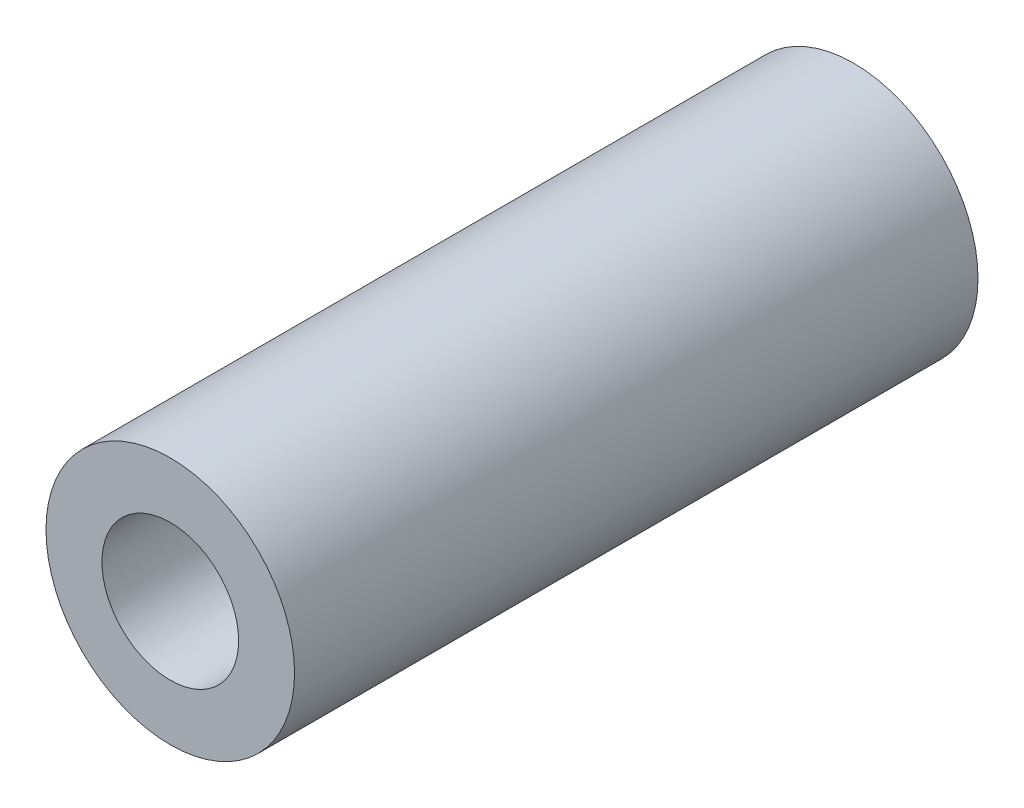
SolidWorks part; units mm, degrees
ref_plane "前视基准面" through (0, 0, 0) normal (0, 0, 1) x (1, 0, 0)
ref_plane "上视基准面" through (0, 0, 0) normal (0, 1, 0) x (1, 0, 0)
ref_plane "右视基准面" through (0, 0, 0) normal (1, 0, 0) x (0, 0, -1)
sketch "草图1" plane through (0, 0, 0) normal (0, 0, 1) x (1, 0, 0)
  circle A0 centre (0, 0) radius 1.1
  circle A1 centre (0, 0) radius 2
extrude "凸台-拉伸1" add sketch "草图1" along normal blind 11
